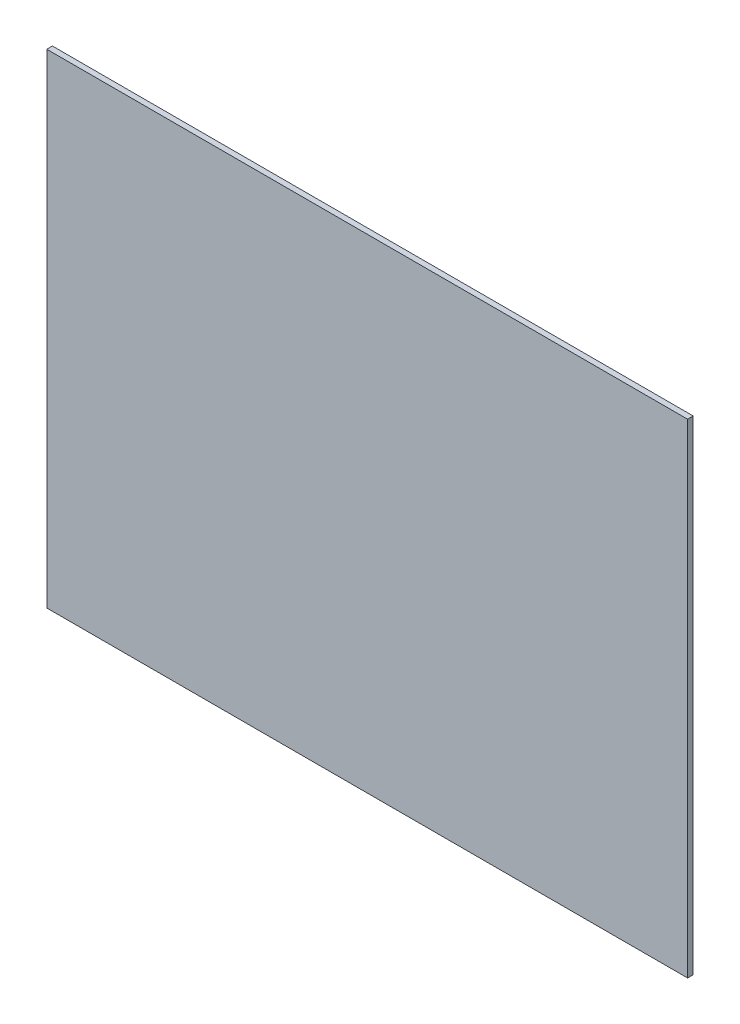
SolidWorks part; units mm, degrees
ref_plane "Front Plane" through (0, 0, 0) normal (0, 0, 1) x (1, 0, 0)
ref_plane "Top Plane" through (0, 0, 0) normal (0, 1, 0) x (1, 0, 0)
ref_plane "Right Plane" through (0, 0, 0) normal (1, 0, 0) x (0, 0, -1)
sketch "Sketch1" plane through (0, 0, 0) normal (0, 0, 1) x (1, 0, 0)
  line L1 (-304.8, 230.1875) -> (304.8, 230.1875)
  line L2 (-304.8, 230.1875) -> (-304.8, -230.1875)
  line L3 (-304.8, -230.1875) -> (304.8, -230.1875)
  line L4 (304.8, 230.1875) -> (304.8, -230.1875)
  line L5 (-304.8, 230.1875) -> (304.8, -230.1875) construction
  line L6 (-304.8, -230.1875) -> (304.8, 230.1875) construction
  point P0 (0, 0)
  dimension "D1" = 460.375
  dimension "D2" = 609.6
extrude "Boss-Extrude1" add sketch "Sketch1" along normal blind 5.334
